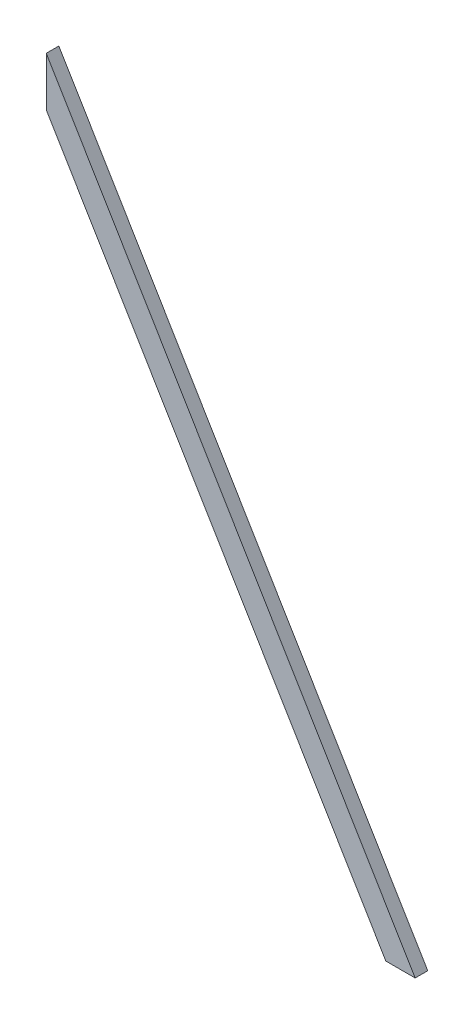
SolidWorks part; units mm, degrees
material "Cedar"
ref_plane "Front Plane" through (0, 0, 0) normal (0, 0, 1) x (1, 0, 0)
ref_plane "Top Plane" through (0, 0, 0) normal (0, 1, 0) x (1, 0, 0)
ref_plane "Right Plane" through (0, 0, 0) normal (1, 0, 0) x (0, 0, -1)
ref_plane "Plane1" through (0, 0, 0) normal (-0.7071, 0, 0.7071) x (0.7071, 0, 0.7071)
sketch "Sketch1" plane through (0, 0, 0) normal (0, 0, 1) x (1, 0, 0)
  line L0 (-18.796, 0) -> (-18.796, 933.6868) construction
  line L1 (-18.796, 0) -> (540.004, 0) construction
  line L2 (540.004, 0) -> (-18.796, 933.6868)
  line L3 (-18.796, 859.496) -> (495.6018, 0)
  line L4 (-18.796, 933.6868) -> (-18.796, 859.496)
  line L5 (495.6018, 0) -> (540.004, 0)
  dimension "D1" = 540.004
  dimension "D2" = 30.9
  dimension "D3" = 38.1
  dimension "D4" = 18.796
extrude "Boss-Extrude1" add sketch "Sketch1" against normal blind 19.05
